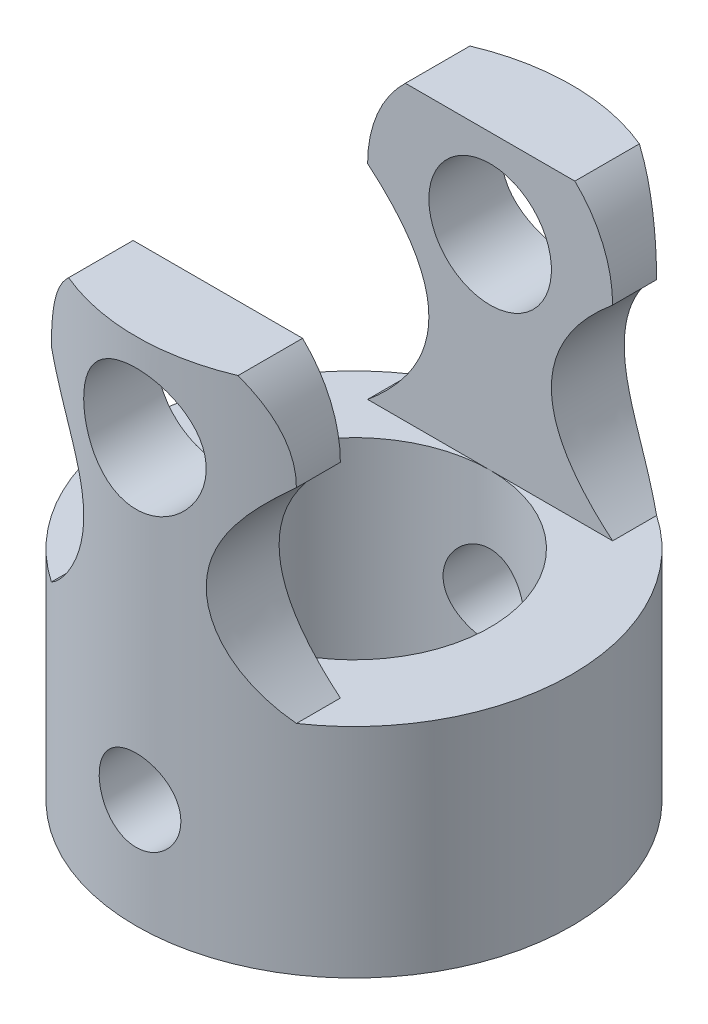
SolidWorks part; units mm, degrees
ref_plane "Front Plane" through (0, 0, 0) normal (0, 0, 1) x (1, 0, 0)
ref_plane "Top Plane" through (0, 0, 0) normal (0, 1, 0) x (1, 0, 0)
ref_plane "Right Plane" through (0, 0, 0) normal (1, 0, 0) x (0, 0, -1)
sketch "Sketch2" plane through (0, 0, 0) normal (0, 1, 0) x (1, 0, 0)
  circle A0 centre (0, 0) radius 5
  circle A1 centre (0, 0) radius 8
  dimension "D1" = 10
  dimension "D2" = 16
extrude "Boss-Extrude1" add sketch "Sketch2" along normal blind 8
sketch "Sketch3" plane through (0, 0, 0) normal (0, 0, 1) x (1, 0, 0)
  line L0 (0, 8) -> (0, 20) construction
  line L1 (8, 8) -> (-8, 8) construction
  line L2 (0, 8) -> (-4.5, 8)
  line L3 (-4.5, 15.5) -> (-4.5, 20) construction
  line L4 (-4.5, 20) -> (4.5, 20)
  line L5 (4.5, 20) -> (4.5, 15.5) construction
  line L6 (5, 8) -> (-5, 8) construction
  line L7 (4.5, 8) -> (0, 8)
  line L8 (-2.25, 15.5) -> (-2.25, 8) construction
  line L9 (2.25, 15.5) -> (2.25, 8) construction
  line L10 (-4.5, 8) -> (-4.5, 15.5) construction
  line L11 (4.5, 15.5) -> (4.5, 8) construction
  arc A0 (4.5, 15.5) -> (-4.5, 15.5) centre (0, 15.5) ccw
  circle A1 centre (0, 15.5) radius 2.25
  spline S0 degree 2 poles (-4.5, 15.5) (0, 11.75) (-4.5, 8) knots 0 0 0 1 1 1
  spline S1 degree 2 poles (4.5, 15.5) (0, 11.75) (4.5, 8) knots 0 0 0 1 1 1
  point P8 (0, 20)
  dimension "D3" = 4.5
  dimension "D1" = 12
  dimension "D2" = 9
extrude "Boss-Extrude2" add sketch "Sketch3" along normal up to surface and the other way up to surface contours S0 L2 L7 S1 A0 | A1 up to face at (0, 8, 8) other way up to face at (0, 8, 8)
sketch "Sketch4" plane through (0, 0, 0) normal (0, -1, 0) x (1, 0, 0)
  circle A0 centre (0, 0) radius 5
extrude "Cut-Extrude1" cut sketch "Sketch4" against normal through all
sketch "Sketch5" plane through (0, 0, 0) normal (1, 0, 0) x (0, 0, -1)
  line L0 (-5, 20) -> (-5, 8)
  line L1 (6.6144, 8) -> (-6.6144, 8) construction
  line L2 (-5, 20) -> (5, 20)
  line L3 (5, 20) -> (5, 8)
  line L4 (5, 8) -> (-5, 8)
extrude "Cut-Extrude2" cut sketch "Sketch5" against normal through all both and the other way through all
sketch "Sketch6" plane through (0, 0, 0) normal (0, 0, 1) x (1, 0, 0)
  line L0 (-8, 4) -> (8, 4) construction
  line L1 (-8, 8) -> (-8, 0) construction
  line L2 (8, 0) -> (8, 8) construction
  circle A0 centre (0, 4) radius 1.5
  dimension "D1" = 3
extrude "Cut-Extrude3" cut sketch "Sketch6" against normal through all both and the other way through all
sketch "Sketch7" plane through (0, 0, 0) normal (0, 0, 1) x (1, 0, 0)
  line L0 (-3.1125, 18.75) -> (3.1125, 18.75)
  line L1 (0, 20) -> (0, 18.75) construction
  arc A0 (4.5, 15.5) -> (-4.5, 15.5) centre (0, 15.5) ccw construction
  arc A1 (3.1125, 18.75) -> (-3.1125, 18.75) centre (0, 15.5) ccw
  dimension "D1" = 1.25
extrude "Cut-Extrude4" cut sketch "Sketch7" against normal through all both and the other way through all
